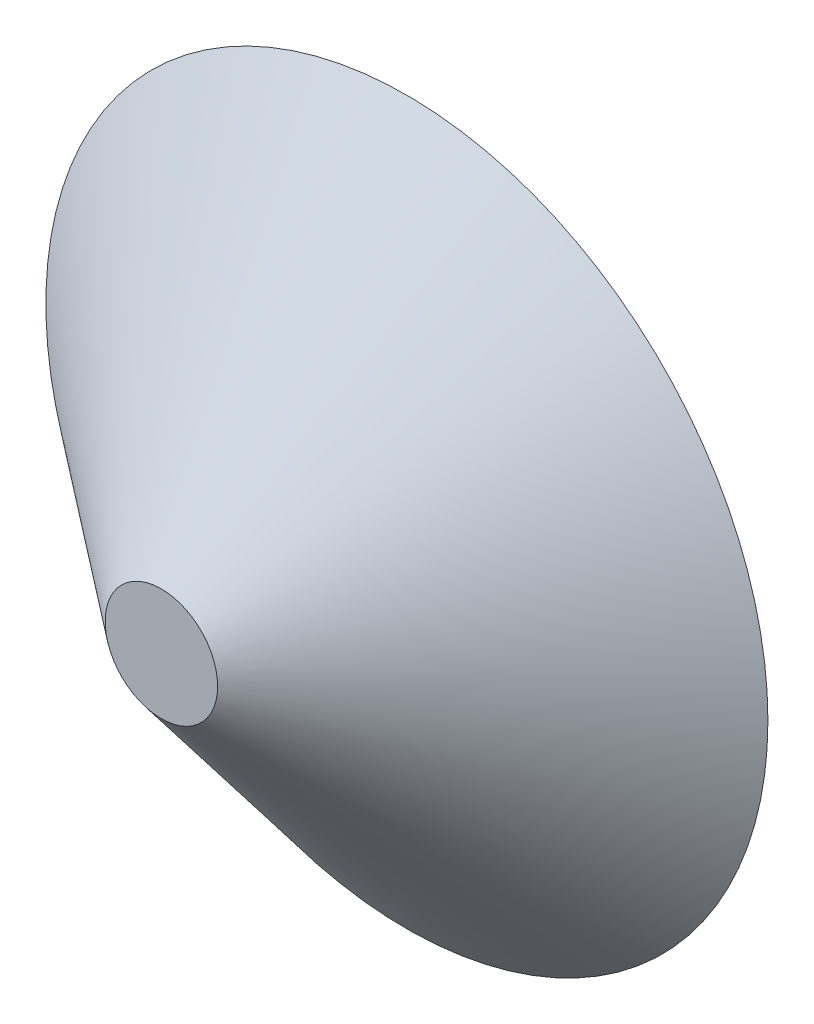
SolidWorks part; units mm, degrees
material "6061-T6 (SS)"
ref_plane "Front" through (0, 0, 0) normal (0, 0, 1) x (1, 0, 0)
ref_plane "Top" through (0, 0, 0) normal (0, 1, 0) x (1, 0, 0)
ref_plane "Right" through (0, 0, 0) normal (1, 0, 0) x (0, 0, -1)
sketch "Sketch1" plane through (0, 0, 0) normal (0, 0, 1) x (1, 0, 0)
  circle A0 centre (0, 0) radius 140
extrude "Boss-Extrude4" add sketch "Sketch1" along normal blind 95.2 draft 51.15 contours A0
shell "Shell5" thickness 1.88
